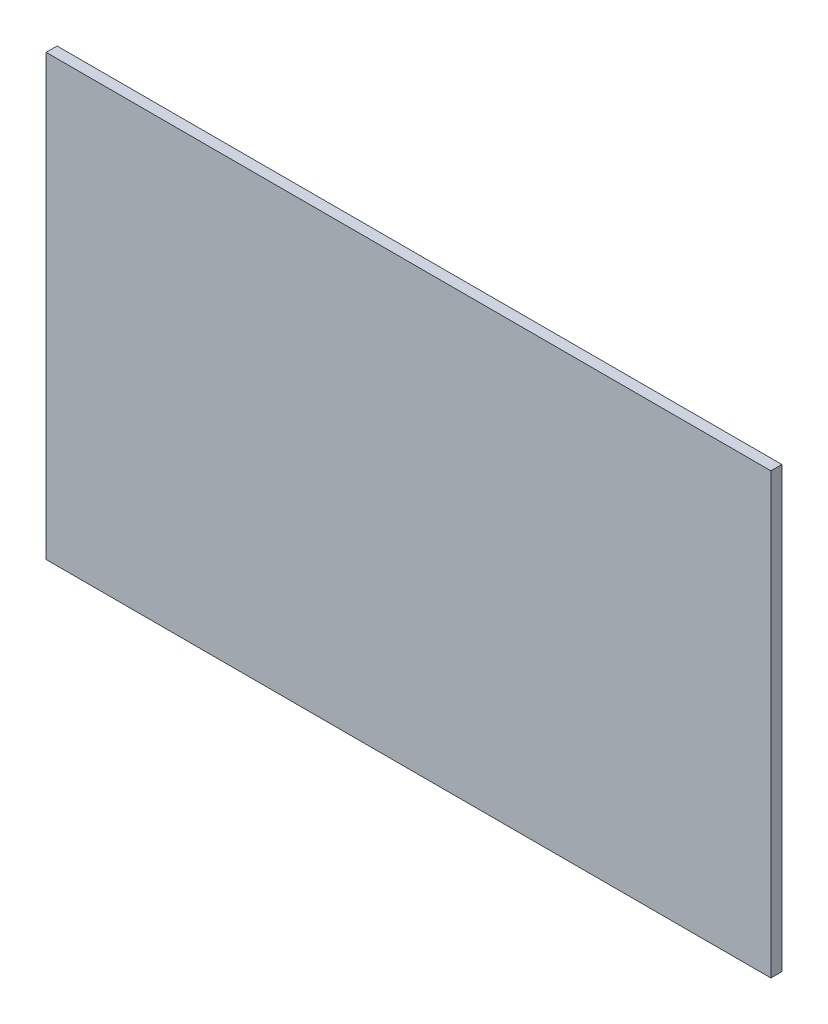
SolidWorks part; units mm, degrees
ref_plane "Front Plane" through (0, 0, 0) normal (0, 0, 1) x (1, 0, 0)
ref_plane "Top Plane" through (0, 0, 0) normal (0, 1, 0) x (1, 0, 0)
ref_plane "Right Plane" through (0, 0, 0) normal (1, 0, 0) x (0, 0, -1)
sketch "Sketch1" plane through (0, 0, 0) normal (0, 0, 1) x (1, 0, 0)
  line L1 (0, 0) -> (5029.2, 0)
  line L2 (0, 0) -> (0, 3048)
  line L3 (0, 3048) -> (5029.2, 3048)
  line L4 (5029.2, 0) -> (5029.2, 3048)
  dimension "D1" = 3048
  dimension "D2" = 5029.2
extrude "Boss-Extrude1" add sketch "Sketch1" along normal blind 76.2
